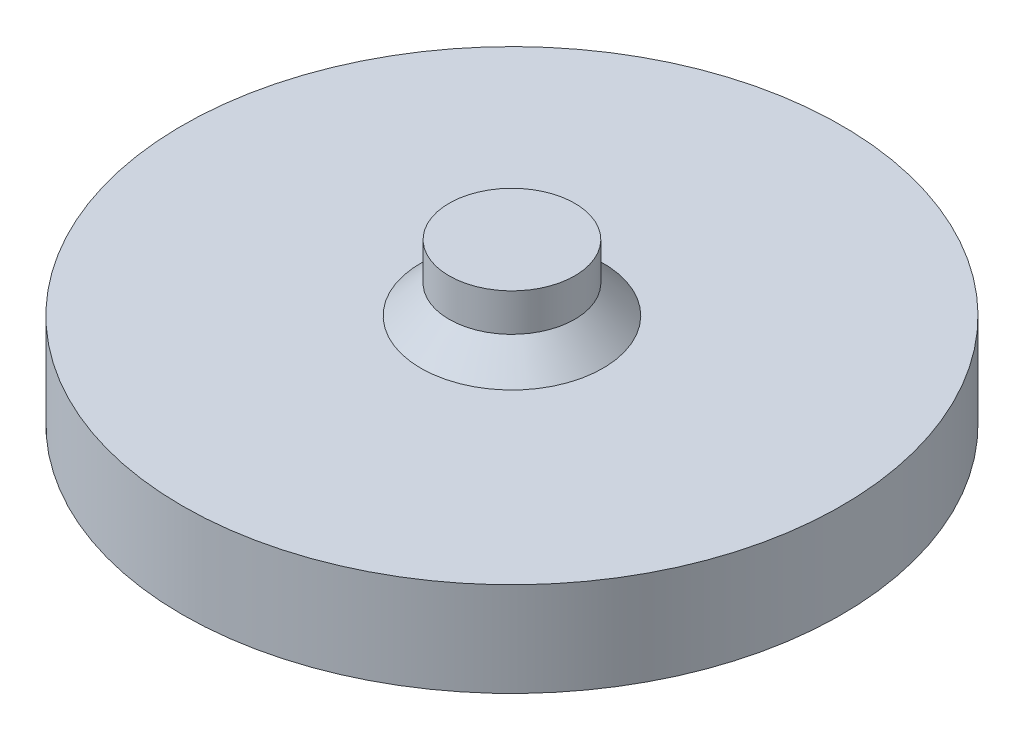
SolidWorks part; units mm, degrees
ref_plane "Front Plane" through (0, 0, 0) normal (0, 0, 1) x (1, 0, 0)
ref_plane "Top Plane" through (0, 0, 0) normal (0, 1, 0) x (1, 0, 0)
ref_plane "Right Plane" through (0, 0, 0) normal (1, 0, 0) x (0, 0, -1)
sketch "Sketch1" plane through (0, 0, 0) normal (0, 1, 0) x (1, 0, 0)
  circle A0 centre (0, 0) radius 70
extrude "Boss-Extrude1" add sketch "Sketch1" along normal blind 20
sketch "Sketch2" plane through (0, 0, 0) normal (0, -1, 0) x (1, 0, 0)
  line L0 (0, 0) -> (0, 59) construction
  line L1 (-4, 56.5) -> (4, 56.5)
  line L2 (-4, 56.5) -> (-4, 61.5)
  line L3 (-4, 61.5) -> (4, 61.5)
  line L4 (4, 56.5) -> (4, 61.5)
  line L5 (-4, 56.5) -> (4, 61.5) construction
  line L6 (-4, 61.5) -> (4, 56.5) construction
  line L7 (50.9304, 24.7859) -> (55.2606, 27.2859)
  line L8 (51.2606, 34.2141) -> (55.2606, 27.2859)
  line L9 (46.9304, 31.7141) -> (51.2606, 34.2141)
  line L10 (46.9304, 31.7141) -> (50.9304, 24.7859)
  line L11 (46.9304, -31.7141) -> (51.2606, -34.2141)
  line L12 (55.2606, -27.2859) -> (51.2606, -34.2141)
  line L13 (50.9304, -24.7859) -> (55.2606, -27.2859)
  line L14 (50.9304, -24.7859) -> (46.9304, -31.7141)
  line L15 (-4, -56.5) -> (-4, -61.5) [skipped]
  line L16 (4, -61.5) -> (-4, -61.5) [skipped]
  line L17 (4, -56.5) -> (4, -61.5) [skipped]
  line L18 (4, -56.5) -> (-4, -56.5) [skipped]
  line L19 (-50.9304, -24.7859) -> (-55.2606, -27.2859)
  line L20 (-51.2606, -34.2141) -> (-55.2606, -27.2859)
  line L21 (-46.9304, -31.7141) -> (-51.2606, -34.2141)
  line L22 (-46.9304, -31.7141) -> (-50.9304, -24.7859)
  line L23 (-46.9304, 31.7141) -> (-51.2606, 34.2141)
  line L24 (-55.2606, 27.2859) -> (-51.2606, 34.2141)
  line L25 (-50.9304, 24.7859) -> (-55.2606, 27.2859)
  line L26 (-50.9304, 24.7859) -> (-46.9304, 31.7141)
  circle A0 centre (0, 0) radius 59 construction
  point P2 (0, 59)
  dimension "D1" = 6
extrude "Cut-Extrude1" cut sketch "Sketch2" against normal blind 6.89
sketch "Sketch3" plane through (0, 20, 0) normal (0, 1, 0) x (1, 0, 0)
  circle A0 centre (0, 0) radius 13.35
  dimension "D1" = 26.7
extrude "Boss-Extrude2" add sketch "Sketch3" along normal blind 14 contours A0
chamfer "Chamfer1" distance 6 angle 45 1 edges at (0, 20, 13.35)
